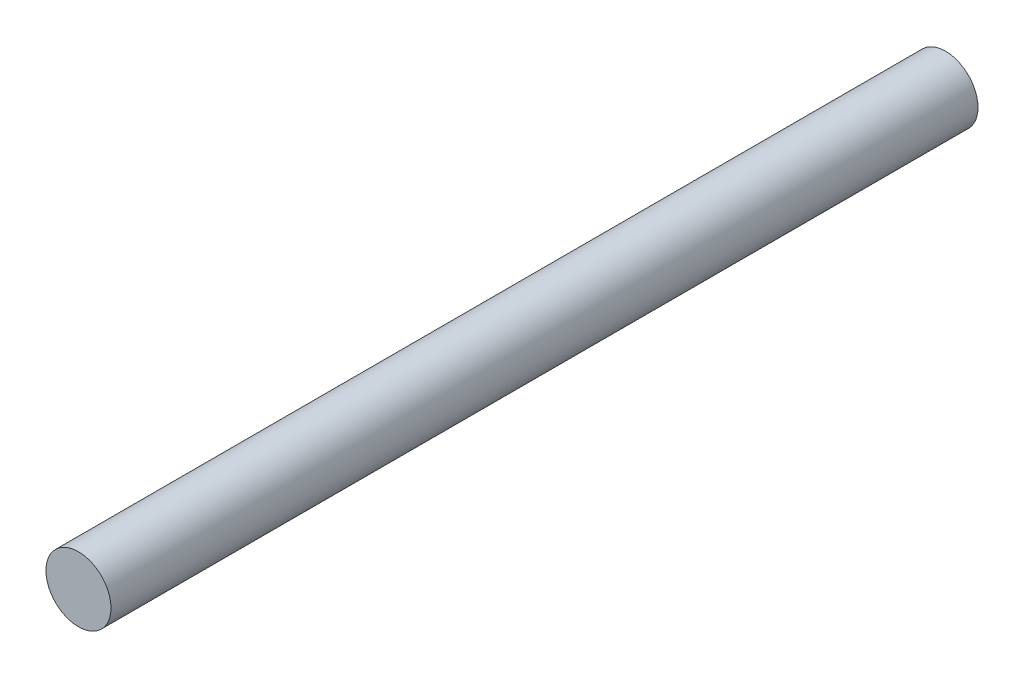
SolidWorks part; units mm, degrees
material "Alloy Steel"
ref_plane "Front Plane" through (0, 0, 0) normal (0, 0, 1) x (1, 0, 0)
ref_plane "Top Plane" through (0, 0, 0) normal (0, 1, 0) x (1, 0, 0)
ref_plane "Right Plane" through (0, 0, 0) normal (1, 0, 0) x (0, 0, -1)
sketch "Sketch2" plane through (0, 0, 0) normal (0, 0, 1) x (1, 0, 0)
  circle A0 centre (0, 0) radius 4.7625
  dimension "D1" = 9.525
extrude "Boss-Extrude1" add sketch "Sketch2" along normal blind 127
